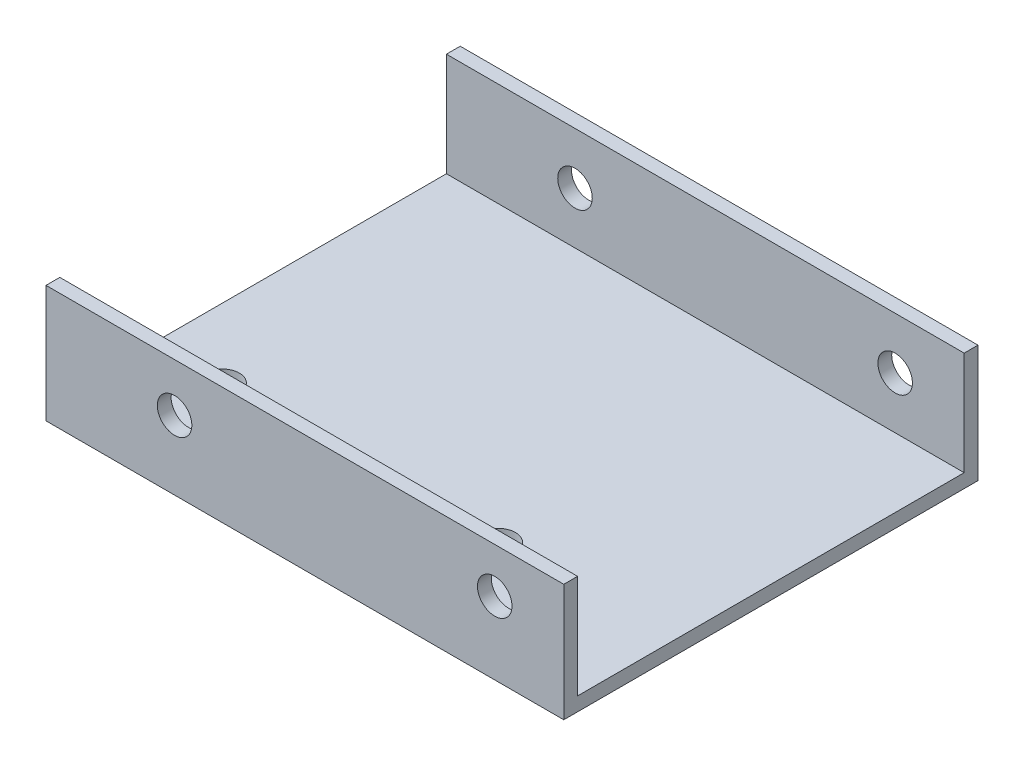
SolidWorks part; units mm, degrees
material "Liga 1060"
ref_plane "Plano frontal" through (0, 0, 0) normal (0, 0, 1) x (1, 0, 0)
ref_plane "Plano superior" through (0, 0, 0) normal (0, 1, 0) x (1, 0, 0)
ref_plane "Plano direito" through (0, 0, 0) normal (1, 0, 0) x (0, 0, -1)
sketch "Esboço1" plane through (0, 0, 0) normal (0, 1, 0) x (1, 0, 0)
  line L1 (37.5, -28) -> (-37.5, -28)
  line L2 (37.5, -28) -> (37.5, 28)
  line L3 (37.5, 28) -> (-37.5, 28)
  line L4 (-37.5, -28) -> (-37.5, 28)
  line L5 (37.5, -28) -> (-37.5, 28) construction
  line L6 (37.5, 28) -> (-37.5, -28) construction
  point P0 (0, 0)
  dimension "D1" = 75
  dimension "D2" = 56
extrude "Ressalto-extrusão1" add sketch "Esboço1" along normal blind 2
sketch "Esboço3" plane through (0, 0, 28) normal (0, 0, 1) x (1, 0, 0)
  line L0 (37.5, 2) -> (37.5, 0) construction
  line L1 (-37.5, 0) -> (37.5, 0)
  line L2 (-37.5, 0) -> (-37.5, 17)
  line L3 (-37.5, 17) -> (37.5, 17)
  line L4 (37.5, 0) -> (37.5, 17)
  dimension "D1" = 17
extrude "Ressalto-extrusão3" add sketch "Esboço3" along normal blind 2
mirror "Espelhar2" about plane through (0, 0, 0) normal (0, 0, 1) of "Ressalto-extrusão3"
sketch "Esboço4" plane through (0, 0, 40) normal (0, 0, 1) x (1, 0, 0)
  line L1 (-37.5, 0) -> (37.5, 0) construction
  line L2 (-37.5, 17) -> (-37.5, 0) construction
  circle A1 centre (-18.875, 10) radius 2.5
  point P6 (-26.9701, 10.1129)
  dimension "D2" = 5
  dimension "D3" = 18.625
  dimension "D1" = 10
extrude "Corte-extrusão1" cut sketch "Esboço4" against normal up to next
sketch "Esboço5" plane through (0, 0, 30) normal (0, 0, 1) x (1, 0, 0)
  line L0 (-37.5, 0) -> (37.5, 0) construction
  line L1 (37.5, 0) -> (37.5, 17) construction
  circle A0 centre (27.5, 10.5) radius 2.5
  dimension "D1" = 5
  dimension "D2" = 10.5
  dimension "D3" = 10
extrude "Corte-extrusão2" cut sketch "Esboço5" against normal up to next
sketch "Esboço6" plane through (0, 0, 0) normal (0, -1, 0) x (1, 0, 0)
  line L0 (37.5, 30) -> (37.5, -30) construction
  line L1 (-37.5, 30) -> (37.5, 30) construction
  circle A1 centre (-27.5, 14.5) radius 2.5 construction
  circle A2 centre (12.5, 14.5) radius 2.5
  circle A3 centre (-27.5, 14.5) radius 2.5
  dimension "D2" = 5
  dimension "D3" = 15.5
  dimension "D1" = 25
extrude "Corte-extrusão3" cut sketch "Esboço6" against normal blind 2
sketch "Sketch1" plane through (0, 0, -30) normal (0, 0, -1) x (-1, 0, 0)
  line L0 (-37.5, 0) -> (-37.5, 17) construction
  line L2 (37.5, 0) -> (-37.5, 0) construction
  circle A0 centre (-27.5, 9.5) radius 2.5
  point P4 (0, 0)
  dimension "D1" = 5
  dimension "D2" = 10
  dimension "D3" = 9.5
extrude "Cut-Extrude1" cut sketch "Sketch1" against normal up to next
sketch "Sketch2" plane through (0, 0, -30) normal (0, 0, -1) x (-1, 0, 0)
  line L0 (37.5, 0) -> (-37.5, 0) construction
  line L1 (37.5, 17) -> (37.5, 0) construction
  circle A0 centre (18.875, 9.5) radius 2.5
  point P6 (0, 0)
  dimension "D1" = 5
  dimension "D2" = 9.5
  dimension "D3" = 18.625
extrude "Cut-Extrude2" cut sketch "Sketch2" against normal up to next
